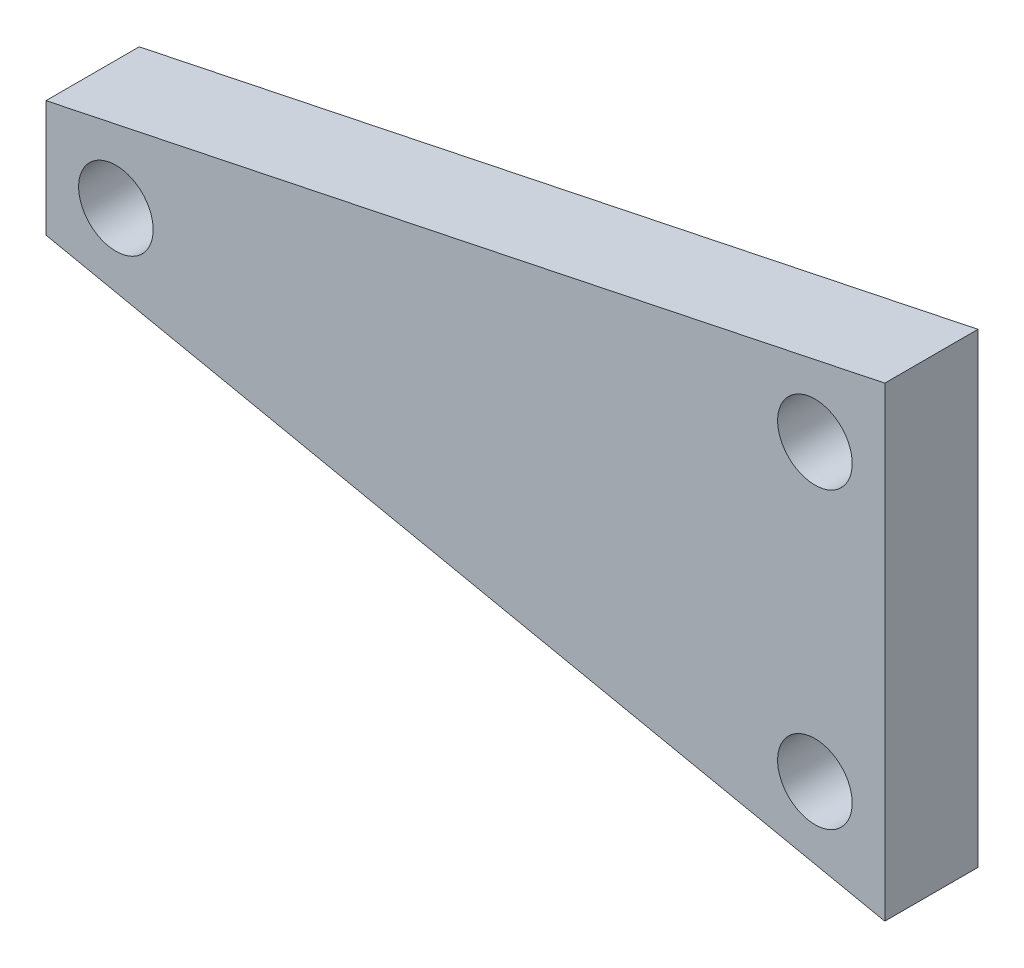
SolidWorks part; units mm, degrees
ref_plane "Front Plane" through (0, 0, 0) normal (0, 0, 1) x (1, 0, 0)
ref_plane "Top Plane" through (0, 0, 0) normal (0, 1, 0) x (1, 0, 0)
ref_plane "Right Plane" through (0, 0, 0) normal (1, 0, 0) x (0, 0, -1)
sketch "Sketch1" plane through (0, 0, 0) normal (0, 0, 1) x (1, 0, 0)
  line L0 (0, 0) -> (0, 5)
  line L1 (0, 5) -> (36, 12.5)
  line L2 (36, 12.5) -> (36, -7.5)
  line L3 (36, -7.5) -> (0, 0)
  circle A0 centre (3, 2.5) radius 1.6
  circle A1 centre (33, 8.8106) radius 1.6
  circle A2 centre (33, -3.8106) radius 1.6
  point P3 (36, 2.5)
  point P6 (0, 2.5)
  point P13 (0, 0)
  point P14 (0, 0)
  point P15 (0, 0)
  dimension "D4" = 3.2
  dimension "D5" = 3
  dimension "D1" = 3
  dimension "D2" = 5
  dimension "D3" = 20
  dimension "D6" = 30
  dimension "D7" = 3
  dimension "D8" = 3
extrude "Boss-Extrude1" add sketch "Sketch1" along normal blind 4
